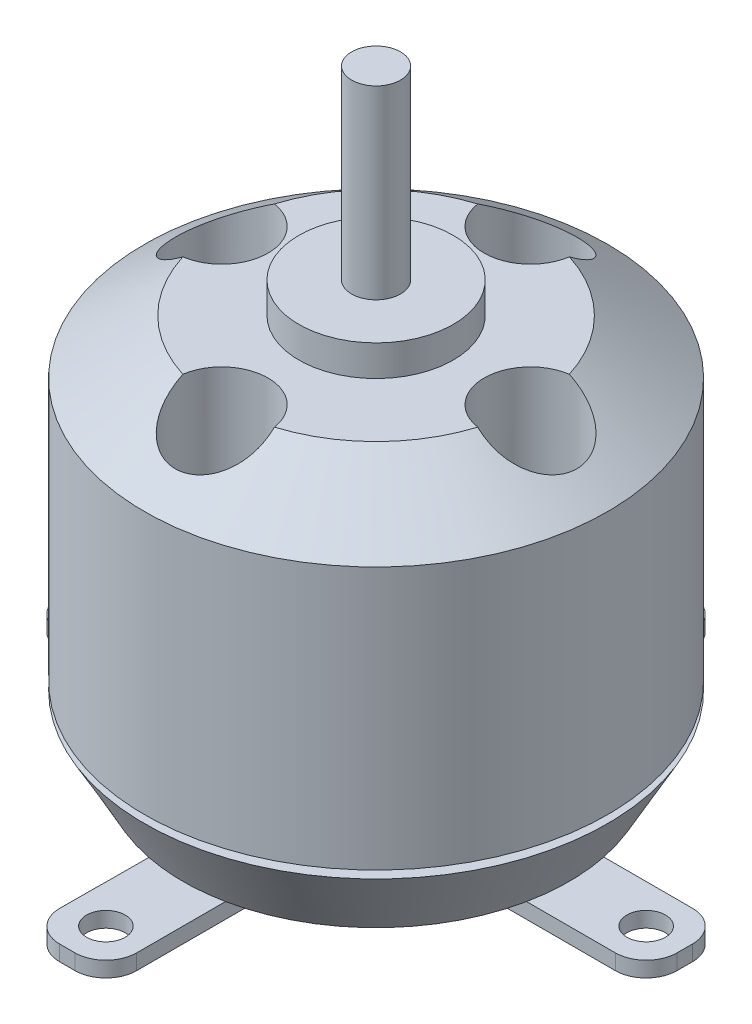
SolidWorks part; units mm, degrees
material "1060 Alloy"
ref_plane "Front Plane" through (0, 0, 0) normal (0, 0, 1) x (1, 0, 0)
ref_plane "Top Plane" through (0, 0, 0) normal (0, 1, 0) x (1, 0, 0)
ref_plane "Right Plane" through (0, 0, 0) normal (1, 0, 0) x (0, 0, -1)
sketch "Sketch1" plane through (0, 0, 0) normal (0, 0, 1) x (1, 0, 0)
  line L0 (0, 0) -> (0, 28.5) construction
  line L1 (0, 0) -> (1.585, 0)
  line L2 (1.585, 0) -> (1.585, 1)
  line L3 (1.585, 1) -> (12.5, 1)
  line L4 (12.5, 1) -> (15, 5.5)
  line L5 (15, 5.5) -> (1.585, 5.5)
  line L6 (1.585, 5.5) -> (1.585, 6)
  line L7 (1.585, 6) -> (15, 6)
  line L8 (15, 6) -> (15, 23)
  line L9 (15, 23) -> (10, 26.5)
  line L10 (10, 26.5) -> (5, 26.5)
  line L11 (5, 26.5) -> (5, 28.5)
  line L12 (5, 28.5) -> (1.585, 28.5)
  line L13 (1.585, 28.5) -> (1.585, 40.5)
  line L14 (1.585, 40.5) -> (0, 40.5)
  line L15 (12.5, 1) -> (15, 1) construction
  line L16 (15, 1) -> (15, 5.5) construction
  line L17 (15, 23) -> (10, 23) construction
  line L18 (10, 23) -> (10, 26.5) construction
  line L19 (10, 26.5) -> (9.9634, 26.6758) construction
  line L20 (0, 28.5) -> (0, 40.5) construction
  line L21 (0, 0) -> (0, 40.5)
  dimension "D1" = 28.5
  dimension "D2" = 1.585
  dimension "D3" = 1
  dimension "D4" = 10.915
  dimension "D5" = 15
  dimension "D6" = 1.585
  dimension "D7" = 2.5
  dimension "D8" = 4.5
  dimension "D9" = 0.5
  dimension "D10" = 17
  dimension "D11" = 5
  dimension "D12" = 3.5
  dimension "D13" = 2
  dimension "D14" = 1.585
  dimension "D15" = 5
  dimension "D16" = 1.585
  dimension "D17" = 3.415
  dimension "D18" = 12
revolve "Electric motor body" add sketch "Sketch1" angle 360 about L21
sketch "Sketch4" plane through (0, 26.5, 0) normal (0, 1, 0) x (1, 0, 0)
  circle A0 centre (0, -10) radius 3
  circle A1 centre (0, 0) radius 10 construction
  circle A2 centre (-10, 0) radius 3
  circle A3 centre (10, 0) radius 3
  circle A4 centre (0, 10) radius 3
  dimension "D1" = 6
  dimension "D2" = 6
  dimension "D3" = 6
  dimension "D4" = 6
extrude "motor cooling system" cut sketch "Sketch4" against normal blind 6
sketch "Sketch6" plane through (0, 1, 0) normal (0, -1, 0) x (1, 0, 0)
  line L0 (-20.0054, 0) -> (19.9946, 0) construction
  line L1 (0, 20) -> (0, -20) construction
  line L2 (19.9946, -0.5) -> (19.9946, 0.5)
  line L3 (17.9946, 2.5) -> (9.9946, 2.5)
  line L4 (2.4946, 10) -> (2.4946, 18)
  line L5 (0.4946, 20) -> (-0.4946, 20)
  line L6 (-2.4946, 17.9892) -> (-2.4518, 10.0403)
  line L7 (-9.9517, 2.5) -> (-18.0054, 2.5)
  line L8 (-20.0054, 0.5) -> (-20.0054, -0.5)
  line L9 (-18.0054, -2.5) -> (-9.9946, -2.5)
  line L10 (-2.4946, -10) -> (-2.4946, -18)
  line L11 (-0.4946, -20) -> (0.4946, -20)
  line L12 (2.4946, -18) -> (2.4946, -10)
  line L13 (9.9946, -2.5) -> (17.9946, -2.5)
  arc A1 (-9.9946, -2.5) -> (-2.4946, -10) centre (-9.9946, -10) cw
  arc A2 (2.4946, -10) -> (9.9946, -2.5) centre (9.9946, -10) cw
  arc A3 (9.9946, 2.5) -> (2.4946, 10) centre (9.9946, 10) cw
  arc A4 (-2.4518, 10.0403) -> (-9.9517, 2.5) centre (-9.9517, 10) cw
  arc A5 (-0.4946, 20) -> (-2.4946, 17.9892) centre (-0.4946, 18) ccw
  arc A6 (2.4946, 18) -> (0.4946, 20) centre (0.4946, 18) ccw
  arc A7 (19.9946, 0.5) -> (17.9946, 2.5) centre (17.9946, 0.5) ccw
  arc A8 (19.9946, -0.5) -> (17.9946, -2.5) centre (17.9946, -0.5) cw
  arc A9 (0.4946, -20) -> (2.4946, -18) centre (0.4946, -18) ccw
  arc A10 (-2.4946, -18) -> (-0.4946, -20) centre (-0.4946, -18) ccw
  arc A11 (-18.0054, 2.5) -> (-20.0054, 0.5) centre (-18.0054, 0.5) ccw
  arc A12 (-20.0054, -0.5) -> (-18.0054, -2.5) centre (-18.0054, -0.5) ccw
  circle A13 centre (0, 0) radius 3
  point P5 (0, 0)
  point P25 (2.4946, 2.5)
  point P30 (-2.5054, 20)
  point P33 (2.4946, 20)
  point P36 (19.9946, 2.5)
  point P39 (19.9946, -2.5)
  point P46 (-20.0054, 2.5)
  point P49 (-20.0054, -2.5)
  dimension "D1" = 5
  dimension "D9" = 7.5
  dimension "D10" = 2
  dimension "D11" = 6
  dimension "D2" = 40
  dimension "D3" = 40
  dimension "D4" = 5
  dimension "D5" = 17.5
  dimension "D6" = 5
  dimension "D7" = 2.5
  dimension "D8" = 2.5
extrude "Motor base holder" add sketch "Sketch6" along normal blind 1
sketch "Sketch9" plane through (0, 0, 0) normal (0, -1, 0) x (1, 0, 0)
  line L0 (-20.0054, 0) -> (19.9946, 0) construction
  line L1 (-20.0054, 0.5) -> (-20.0054, -0.5) construction
  line L2 (19.9946, -0.5) -> (19.9946, 0.5) construction
  line L3 (0, 20) -> (0, -20) construction
  line L4 (0.4946, 20) -> (-0.4946, 20) construction
  line L5 (-0.4946, -20) -> (0.4946, -20) construction
  circle A0 centre (-17.5054, 0) radius 1.25
  circle A1 centre (17.4946, 0) radius 1.25
  circle A2 centre (0, -17.5) radius 1.25
  circle A3 centre (0, 17.5) radius 1.25
  circle A4 centre (7, 0) radius 1.5
  circle A5 centre (0, -7) radius 1.5
  circle A6 centre (-7, 0) radius 1.5
  circle A7 centre (0, 7) radius 1.5
  dimension "D1" = 2.5
  dimension "D2" = 2.5
  dimension "D3" = 2.5
  dimension "D4" = 2.5
  dimension "D9" = 3
  dimension "D10" = 3
  dimension "D11" = 3
  dimension "D12" = 3
  dimension "D5" = 2.5
  dimension "D6" = 2.5
  dimension "D7" = 2.5
  dimension "D8" = 2.5
  dimension "D13" = 7
  dimension "D14" = 7
  dimension "D15" = 7
  dimension "D16" = 7
extrude "Screws cut" cut sketch "Sketch9" against normal blind 2
